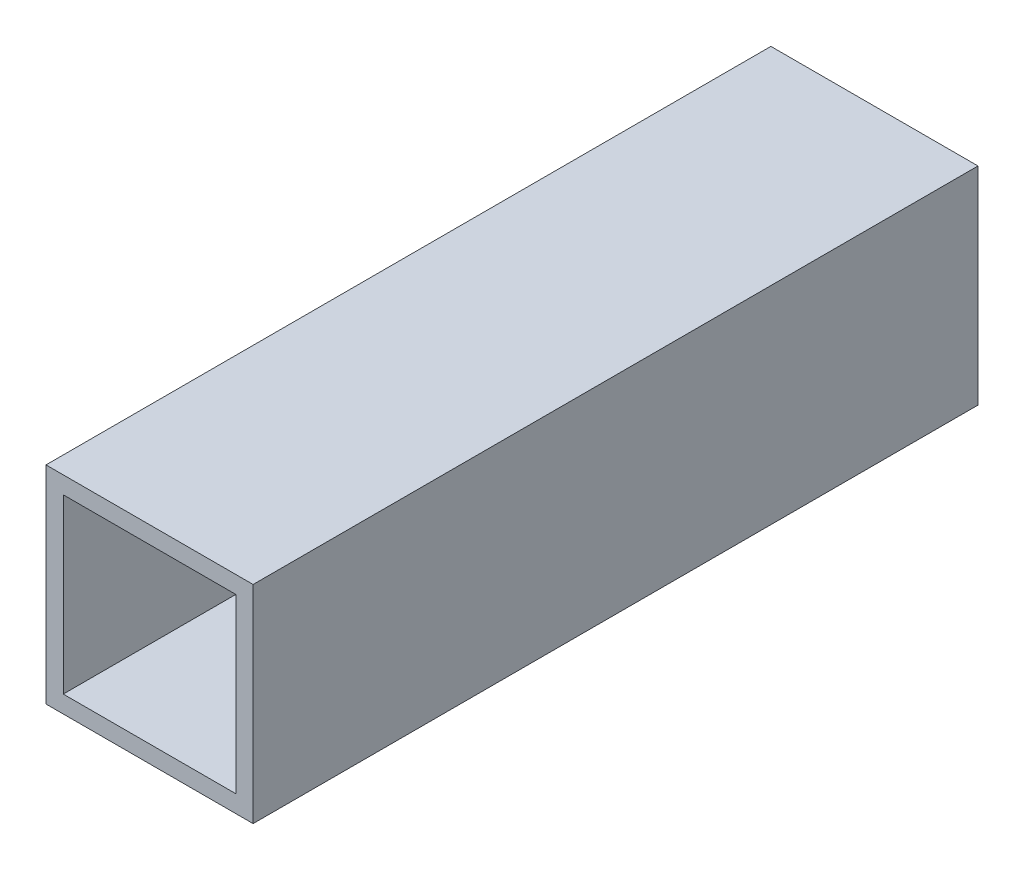
SolidWorks part; units mm, degrees
material "Titanium"
ref_plane "Front Plane" through (0, 0, 0) normal (0, 0, 1) x (1, 0, 0)
ref_plane "Top Plane" through (0, 0, 0) normal (0, 1, 0) x (1, 0, 0)
ref_plane "Right Plane" through (0, 0, 0) normal (1, 0, 0) x (0, 0, -1)
sketch "Sketch1" plane through (0, 0, 0) normal (0, 1, 0) x (1, 0, 0)
  line L1 (-19.05, 66.675) -> (19.05, 66.675)
  line L2 (-19.05, 66.675) -> (-19.05, -66.675)
  line L3 (-19.05, -66.675) -> (19.05, -66.675)
  line L4 (19.05, 66.675) -> (19.05, -66.675)
  dimension "D1" = 19.05
  dimension "D2" = 19.05
  dimension "D3" = 66.675
  dimension "D4" = 66.675
extrude "Boss-Extrude1" add sketch "Sketch1" along normal mid plane 38.1
sketch "Sketch2" plane through (0, 0, 66.675) normal (0, 0, 1) x (1, 0, 0)
  line L0 (-19.05, 19.05) -> (-19.05, -19.05) construction
  line L1 (-15.875, 15.875) -> (15.875, 15.875)
  line L2 (-15.875, 15.875) -> (-15.875, -15.875)
  line L3 (-15.875, -15.875) -> (15.875, -15.875)
  line L4 (15.875, 15.875) -> (15.875, -15.875)
  line L5 (19.05, 19.05) -> (19.05, -19.05) construction
  line L6 (-19.05, -19.05) -> (19.05, -19.05) construction
  line L7 (-19.05, 19.05) -> (19.05, 19.05) construction
  dimension "D1" = 3.175
  dimension "D2" = 3.175
  dimension "D3" = 3.175
  dimension "D4" = 3.175
extrude "Cut-Extrude1" cut sketch "Sketch2" against normal through all
